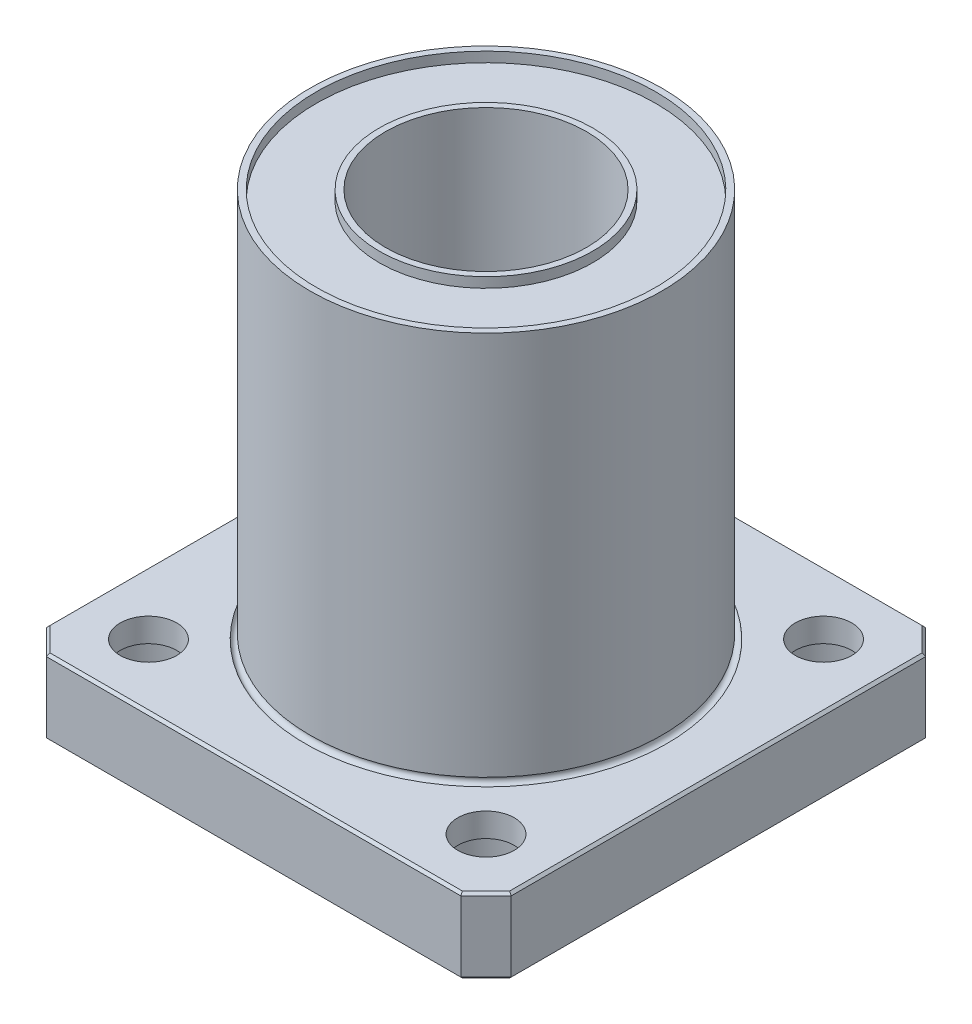
SolidWorks part; units mm, degrees
ref_plane "Front Plane" through (0, 0, 0) normal (0, 0, 1) x (1, 0, 0)
ref_plane "Top Plane" through (0, 0, 0) normal (0, 1, 0) x (1, 0, 0)
ref_plane "Right Plane" through (0, 0, 0) normal (1, 0, 0) x (0, 0, -1)
sketch "Sketch5" plane through (0, 0, 0) normal (1, 0, 0) x (0, 0, -1)
  line L0 (0, 0) -> (0, 30) construction
  line L1 (8.5, 37) -> (8, 37)
  line L2 (14, 0) -> (14, 37)
  line L3 (14, 37) -> (13.5, 37)
  line L4 (13.5, 37) -> (13.5, 36.2)
  line L5 (13.5, 36.2) -> (8.5, 36.2)
  line L6 (8.5, 36.2) -> (8.5, 37)
  line L7 (14, 7.7505) -> (-14, 7.7505) construction
  line L9 (8, 37) -> (8, 0)
  line L10 (8, 0) -> (8.5, 0)
  line L11 (8.5, 0) -> (8.5, 0.8)
  line L12 (8.5, 0.8) -> (13.5, 0.8)
  line L13 (13.5, 0.8) -> (13.5, 0)
  line L14 (13.5, 0) -> (14, 0)
  line L15 (-14, 7.7505) -> (-14, 0) construction
  line L17 (-8, 0) -> (-8, 10.4788) construction
  line L18 (-8, 10.4788) -> (8, 10.4788) construction
  point P2 (0, 10.4788)
  point P18 (0, 7.7505)
  dimension "D1" = 16
  dimension "D2" = 0.5
  dimension "D3" = 0.8
  dimension "D4" = 28
  dimension "D5" = 37
revolve "Bearing Body" add sketch "Sketch5" angle 360 about L0
sketch "Sketch8" plane through (0, 0, 0) normal (0, 1, 0) x (1, 0, 0)
  line L0 (0, -10.5) -> (0, -18.5) construction
  line L1 (18.5, 18.5) -> (-18.5, 18.5) construction
  line L2 (18.5, 18.5) -> (18.5, -18.5) construction
  line L3 (18.5, -18.5) -> (-18.5, -18.5) construction
  line L4 (-18.5, 18.5) -> (-18.5, -18.5) construction
  line L5 (18.5, 18.5) -> (-18.5, -18.5) construction
  line L6 (18.5, -18.5) -> (-18.5, 18.5) construction
  line L7 (0, -18.5) -> (-16.5, -18.5)
  line L8 (-16.5, -18.5) -> (-18.5, -16.5)
  line L9 (-18.5, -16.5) -> (-18.5, 0)
  line L10 (-18.5, 0) -> (-10.5, 0) construction
  line L11 (0, 0) -> (0.0644, 0.2794) construction
  line L12 (-18.5, -16.5) -> (-18.5, -18.5) construction
  line L13 (-18.5, -18.5) -> (-16.5, -18.5) construction
  line L14 (-18.5, 0) -> (-18.5, 16.5)
  line L15 (-18.5, 16.5) -> (-16.5, 18.5)
  line L16 (-16.5, 18.5) -> (0, 18.5)
  line L17 (-10.5, 0) -> (-18.5, 0) construction
  line L18 (0, 18.5) -> (0, 10.5) construction
  line L19 (0, 0) -> (0.2794, -0.0644) construction
  line L20 (0, 18.5) -> (16.5, 18.5)
  line L21 (16.5, 18.5) -> (18.5, 16.5)
  line L22 (18.5, 16.5) -> (18.5, 0)
  line L23 (0, 10.5) -> (0, 18.5) construction
  line L24 (18.5, 0) -> (10.5, 0) construction
  line L25 (0, 0) -> (-0.0644, -0.2794) construction
  line L26 (18.5, 0) -> (18.5, -16.5)
  line L27 (18.5, -16.5) -> (16.5, -18.5)
  line L28 (16.5, -18.5) -> (0, -18.5)
  line L29 (10.5, 0) -> (18.5, 0) construction
  line L30 (0, -18.5) -> (0, -10.5) construction
  line L31 (0, 0) -> (-0.2794, 0.0644) construction
  circle A0 centre (0, 0) radius 10.5 construction
  arc A1 (-10.5, 0) -> (0, -10.5) centre (0, 0) ccw
  arc A2 (0, 10.5) -> (-10.5, 0) centre (0, 0) ccw
  arc A3 (10.5, 0) -> (0, 10.5) centre (0, 0) ccw
  arc A4 (0, -10.5) -> (10.5, 0) centre (0, 0) ccw
  point P38 (0, 0)
  dimension "D1" = 37
  dimension "D2" = 2
  dimension "D3" = 4
extrude "Flange" add sketch "Sketch8" along normal blind 6
sketch "Sketch9" plane through (0, 0, 0) normal (0, -1, 0) x (-1, 0, 0)
  line L0 (0, 0) -> (16, -16) construction
  line L1 (0, 0) -> (50000, 0) construction
  circle A0 centre (0, 0) radius 19 construction
  circle A1 centre (13.435, -13.435) radius 4
  circle A2 centre (-13.435, -13.435) radius 4
  circle A3 centre (-13.435, 13.435) radius 4
  circle A4 centre (13.435, 13.435) radius 4
  point P16 (0, 0)
  dimension "D1" = 38
  dimension "D2" = 8
  dimension "D4" = 45
  dimension "D3" = 4
extrude "Counterbore" cut sketch "Sketch9" against normal blind 4.1
sketch "Sketch10" plane through (0, 4.1, 0) normal (0, -1, 0) x (-1, 0, 0)
  circle A0 centre (13.435, 13.435) radius 2.25
  circle A1 centre (13.435, -13.435) radius 2.25
  circle A2 centre (-13.435, -13.435) radius 2.25
  circle A3 centre (-13.435, 13.435) radius 2.25
  point P12 (0, 0)
  dimension "D1" = 4
extrude "Mounting Holes" cut sketch "Sketch10" against normal through all
sketch "Sketch11" plane through (0, 0, 0) normal (1, 0, 0) x (0, 0, -1)
  line L0 (0, 0) -> (0, 50000) construction
  line L1 (14, 37) -> (-14, 37) construction
  line L3 (-16, 6) -> (16, 6) construction
  line L4 (10.5, 6) -> (-14.0261, 6) construction
  line L6 (-14, 37) -> (-14.0261, 6) construction
  line L8 (-16.5, 6) -> (16.5, 6) construction
  line L9 (-16.5, 6) -> (16.5, 6) construction
  circle A0 centre (-14.0261, 6) radius 0.375
  dimension "D3" = 0.75
revolve "Relief" cut sketch "Sketch11" angle 360 about L0
chamfer "Chamfer1" distance 0.2 angle 45 16 edges at (17.5, 0, -17.5) (18.5, 0, 0) (17.5, 0, 17.5) (0, 0, 18.5) (-17.5, 0, 17.5) (-18.5, 0, 0) (0, 0, -18.5) (-17.5, 0, -17.5) (-17.5, 6, -17.5) (0, 6, -18.5) (17.5, 6, -17.5) (18.5, 6, 0) (17.5, 6, 17.5) (0, 6, 18.5) (-17.5, 6, 17.5) (-18.5, 6, 0)
